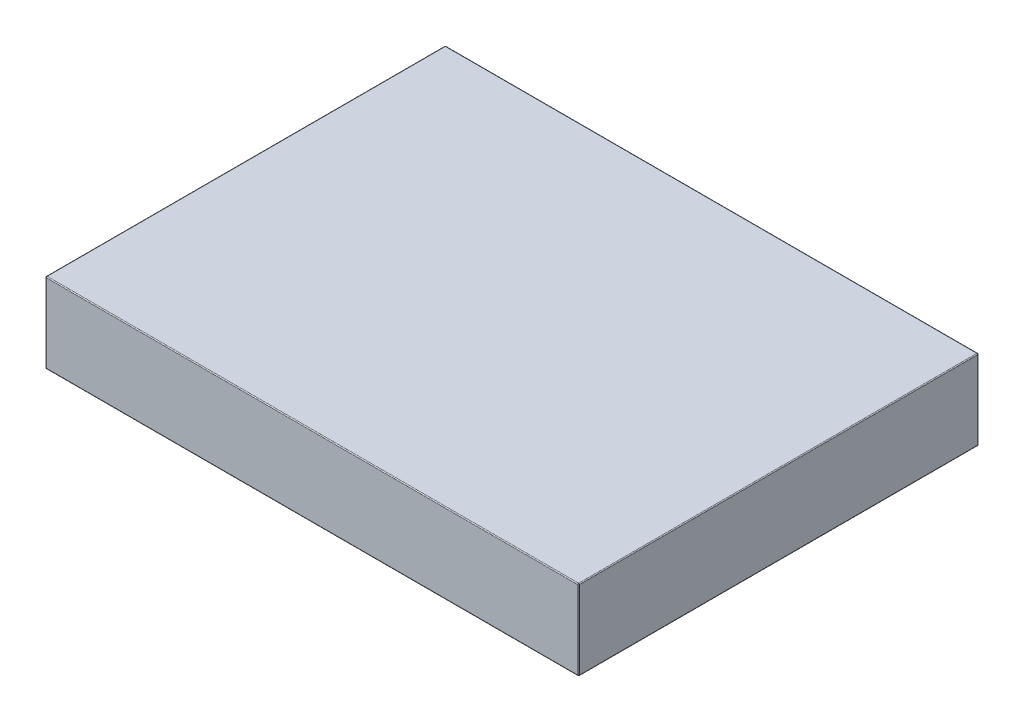
SolidWorks part; units mm, degrees
ref_plane "Front Plane" through (0, 0, 0) normal (0, 0, 1) x (1, 0, 0)
ref_plane "Top Plane" through (0, 0, 0) normal (0, 1, 0) x (1, 0, 0)
ref_plane "Right Plane" through (0, 0, 0) normal (1, 0, 0) x (0, 0, -1)
sketch "Sketch1" plane through (0, 0, 0) normal (0, 1, 0) x (1, 0, 0)
  line L1 (-76.2, 57.15) -> (76.2, 57.15)
  line L2 (-76.2, 57.15) -> (-76.2, -57.15)
  line L3 (-76.2, -57.15) -> (76.2, -57.15)
  line L4 (76.2, 57.15) -> (76.2, -57.15)
  line L5 (-76.2, 57.15) -> (76.2, -57.15) construction
  line L6 (-76.2, -57.15) -> (76.2, 57.15) construction
  point P0 (0, 0)
  dimension "D1" = 152.4
  dimension "D2" = 114.3
extrude "Boss-Extrude1" add sketch "Sketch1" along normal mid plane 22.86
fillet "Fillet1" radius 0.254 12 edges at (-76.2, -11.43, 0) (-76.2, 0, -57.15) (0, -11.43, -57.15) (76.2, 0, -57.15) (76.2, -11.43, 0) (-76.2, 0, 57.15) (76.2, 0, 57.15) (0, -11.43, 57.15) (0, 11.43, 57.15) (-76.2, 11.43, 0) (0, 11.43, -57.15) (76.2, 11.43, 0)
